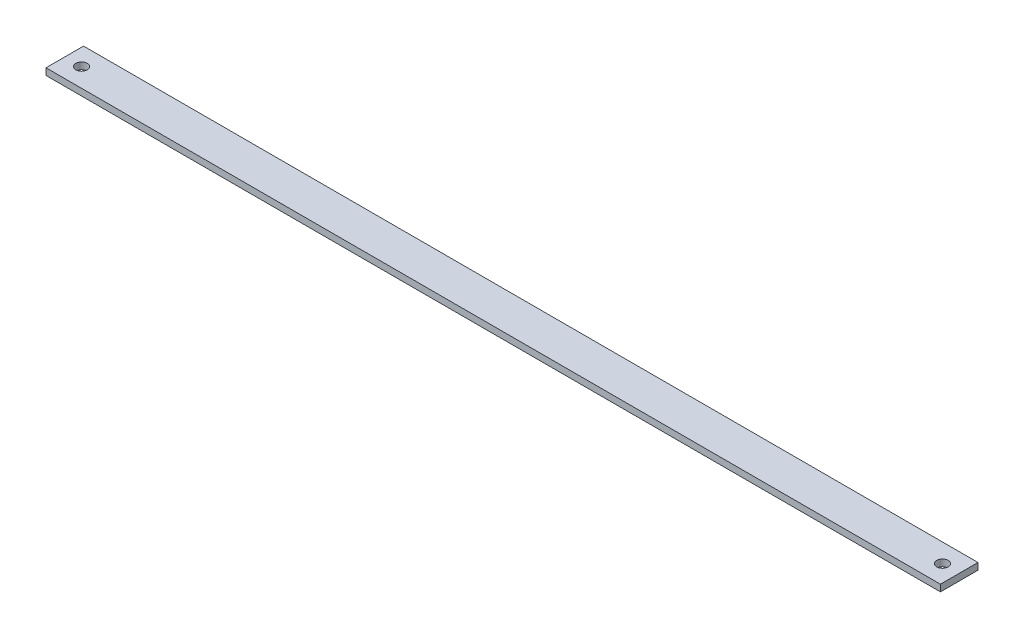
SolidWorks part; units mm, degrees
ref_plane "Front Plane" through (0, 0, 0) normal (0, 0, 1) x (1, 0, 0)
ref_plane "Top Plane" through (0, 0, 0) normal (0, 1, 0) x (1, 0, 0)
ref_plane "Right Plane" through (0, 0, 0) normal (1, 0, 0) x (0, 0, -1)
sketch "Sketch1" plane through (0, 0, 0) normal (0, 1, 0) x (1, 0, 0)
  line L1 (-200, 8.4) -> (200, 8.4)
  line L2 (-200, 8.4) -> (-200, -8.4)
  line L3 (-200, -8.4) -> (200, -8.4)
  line L4 (200, 8.4) -> (200, -8.4)
  line L5 (-200, 8.4) -> (200, -8.4) construction
  line L6 (-200, -8.4) -> (200, 8.4) construction
  circle A0 centre (-192.5, 0) radius 2.55
  circle A1 centre (192.5, 0) radius 2.55
  point P0 (0, 0)
  dimension "D3" = 7.5
  dimension "D4" = 7.5
  dimension "D1" = 400
  dimension "D2" = 16.8
extrude "Boss-Extrude1" add sketch "Sketch1" along normal blind 3
